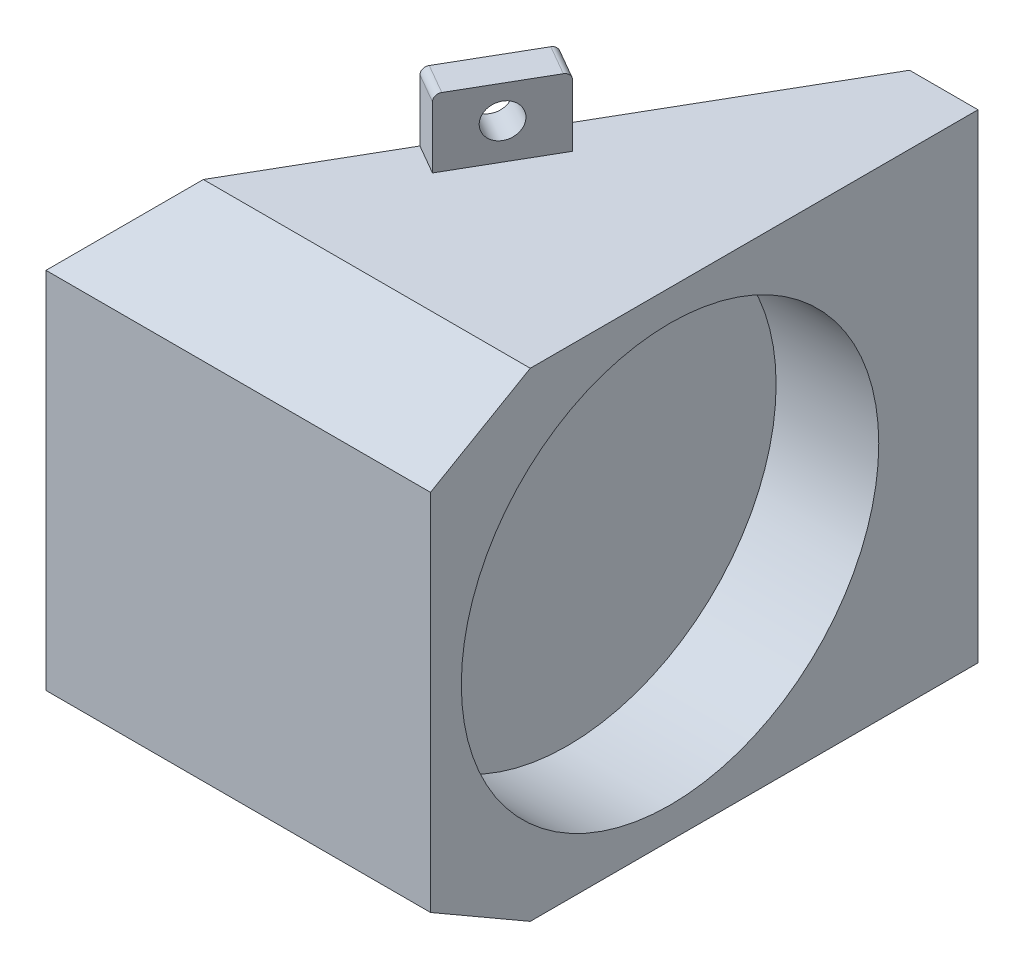
SolidWorks part; units mm, degrees
ref_plane "Front Plane" through (0, 0, 0) normal (0, 0, 1) x (1, 0, 0)
ref_plane "Top Plane" through (0, 0, 0) normal (0, 1, 0) x (1, 0, 0)
ref_plane "Right Plane" through (0, 0, 0) normal (1, 0, 0) x (0, 0, -1)
sketch "Sketch1" plane through (0, 0, 0) normal (0, 1, 0) x (1, 0, 0)
  line L3 (0, 0) -> (0, 101.6)
  line L4 (0, 101.6) -> (-58.6588, 0)
  line L5 (-58.6588, 0) -> (0, 0)
  dimension "D1" = 30
  dimension "D2" = 101.6
extrude "Boss-Extrude1" add sketch "Sketch1" along normal blind 88.9
sketch "Sketch2" plane through (0, 0, 0) normal (1, 0, 0) x (0, 0, -1)
  line L0 (0, 0) -> (101.6, 0) construction
  line L1 (0, 88.9) -> (0, 0) construction
  circle A0 centre (44.45, 44.45) radius 38.735
  dimension "D1" = 77.47
  dimension "D2" = 44.45
  dimension "D3" = 44.45
extrude "Cut-Extrude1" cut sketch "Sketch2" against normal blind 6.35
sketch "Sketch3" plane through (0, 0, 0) normal (1, 0, 0) x (0, 0, -1)
  line L4 (0, 0) -> (101.6, 0)
  line L5 (101.6, 0) -> (101.6, 88.9)
  line L6 (101.6, 88.9) -> (0, 88.9)
  line L7 (0, 88.9) -> (0, 0)
  line L8 (0, 0) -> (101.6, 0)
  line L9 (101.6, 0) -> (101.6, 88.9)
  line L10 (101.6, 88.9) -> (0, 88.9)
  line L11 (0, 88.9) -> (0, 0)
  circle A0 centre (44.45, 44.45) radius 38.735 construction
  circle A1 centre (44.45, 44.45) radius 38.735
  dimension "D1" = 0
extrude "Boss-Extrude2" add sketch "Sketch3" along normal blind 12.7
sketch "Sketch4" plane through (0, 0, 0) normal (0, 0, 1) x (1, 0, 0)
sketch "Sketch5" plane through (0, 0, 0) normal (0, -1, 0) x (1, 0, 0)
  line L0 (-23.1976, -61.4206) -> (-32.7226, -44.9228)
  line L1 (0, -101.6) -> (-58.6588, 0) construction
  line L2 (-32.7226, -44.9228) -> (-27.2233, -41.7478)
  line L3 (-27.2233, -41.7478) -> (-17.6983, -58.2456)
  line L4 (-17.6983, -58.2456) -> (-23.1976, -61.4206)
  dimension "D1" = 19.05
  dimension "D2" = 6.35
extrude "Boss-Extrude4" add sketch "Sketch5" along normal blind 12.7
sketch "Sketch6" plane through (-38.4948, 0, -22.225) normal (0.866, 0, 0.5) x (0.5, 0, -0.866)
  line L0 (41.593, -12.7) -> (41.593, 0) construction
  circle A0 centre (32.068, -6.4637) radius 3.175
  dimension "D1" = 6.35
  dimension "D2" = 9.525
extrude "Cut-Extrude2" cut sketch "Sketch6" against normal through all
sketch "Sketch7" plane through (0, 88.9, 0) normal (0, 1, 0) x (1, 0, 0)
  line L0 (-23.7338, 60.4919) -> (-18.2345, 57.3169)
  line L1 (0, 101.6) -> (-58.6588, 0) construction
  line L2 (-18.2345, 57.3169) -> (-27.7595, 40.8191)
  line L3 (-27.7595, 40.8191) -> (-33.2588, 43.9941)
  line L4 (-33.2588, 43.9941) -> (-23.7338, 60.4919)
  dimension "D1" = 19.05
  dimension "D2" = 6.35
  dimension "D3" = 50.8
extrude "Boss-Extrude5" add sketch "Sketch7" along normal blind 12.7
sketch "Sketch8" plane through (-38.4948, 0, -22.225) normal (0.866, 0, 0.5) x (0.5, 0, -0.866)
  line L0 (40.5206, 101.6) -> (40.5206, 88.9) construction
  circle A0 centre (30.9956, 95.5414) radius 3.175
  dimension "D1" = 6.35
  dimension "D2" = 9.525
extrude "Cut-Extrude3" cut sketch "Sketch8" against normal through all
fillet "Fillet1" radius 1.27 4 edges at (-29.973, -12.7, -43.3353) (-20.448, -12.7, -59.8331) (-30.5092, 101.6, -42.4066) (-20.9842, 101.6, -58.9044)
sketch "Sketch9" plane through (12.7, 0, 0) normal (1, 0, 0) x (0, 0, -1)
  line L0 (18.5092, 88.9) -> (0, 78.2137)
  line L1 (101.6, 88.9) -> (0, 88.9) construction
  line L2 (0, 88.9) -> (0, 0) construction
  line L3 (0, 78.2137) -> (0, 88.9)
  line L4 (0, 88.9) -> (18.5092, 88.9)
  line L5 (0, 44.45) -> (101.6, 44.45) construction
  line L6 (101.6, 0) -> (101.6, 88.9) construction
  line L7 (0, 10.6863) -> (0, 0)
  line L8 (18.5092, 0) -> (0, 10.6863)
  line L9 (0, 0) -> (18.5092, 0)
  dimension "D1" = 30
extrude "Cut-Extrude4" cut sketch "Sketch9" against normal through all
